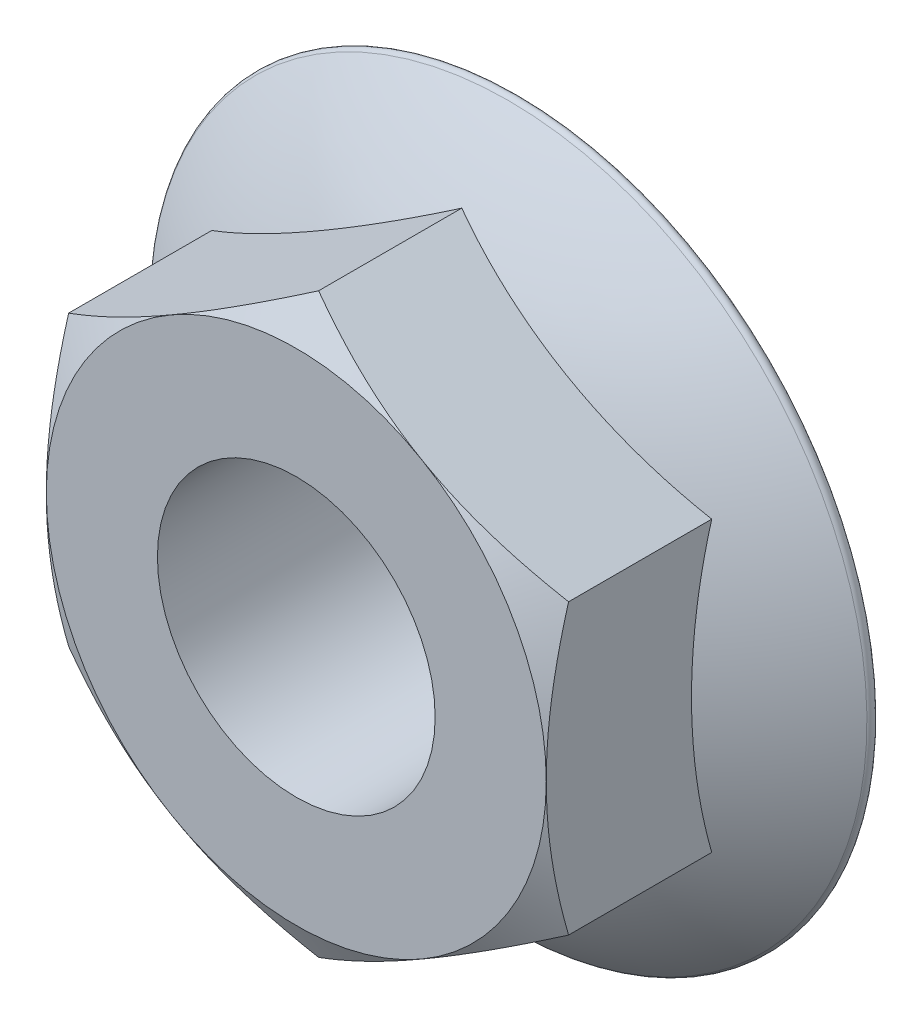
SolidWorks part; units mm, degrees
ref_plane "前视基准面" through (0, 0, 0) normal (0, 0, 1) x (1, 0, 0)
ref_plane "上视基准面" through (0, 0, 0) normal (0, 1, 0) x (1, 0, 0)
ref_plane "右视基准面" through (0, 0, 0) normal (1, 0, 0) x (0, 0, -1)
other "Configuration Table"
sketch "草图1" plane through (0, 0, 0) normal (0, 0, 1) x (1, 0, 0)
  line L1 (22.5, -12.9904) -> (22.5, 12.9904)
  line L2 (22.5, 12.9904) -> (0, 25.9808)
  line L3 (0, 25.9808) -> (-22.5, 12.9904)
  line L4 (-22.5, 12.9904) -> (-22.5, -12.9904)
  line L5 (-22.5, -12.9904) -> (0, -25.9808)
  line L6 (0, -25.9808) -> (22.5, -12.9904)
  circle A0 centre (0, 0) radius 22.5 construction
  dimension "D1" = 45
extrude "凸台-拉伸1" add sketch "草图1" along normal blind 20
sketch "草图2" plane through (0, 0, 0) normal (1, 0, 0) x (0, 0, -1)
  line L0 (0, 0) -> (-12, 0)
  line L1 (0, -31.95) -> (0, 0)
  arc A0 (-12, 0) -> (-0.894, -32.2578) centre (40.4001, 0) ccw
  arc A1 (-0.894, -32.2578) -> (0, -31.95) centre (-0.5, -31.95) ccw
  dimension "D2" = 0.5
  dimension "D1" = 12
  dimension "D3" = 31.95
revolve "旋转1" add sketch "草图2" angle 360 about L0
sketch "草图3" plane through (0, 0, 20) normal (0, 0, 1) x (1, 0, 0)
  circle A0 centre (0, 0) radius 22.5
extrude "切除-拉伸2" cut sketch "草图3" against normal blind 20 draft 60 flip side to cut
sketch "草图4" plane through (0, 0, 20) normal (0, 0, 1) x (1, 0, 0)
  circle A0 centre (0, 0) radius 12.5
  dimension "D1" = 25
extrude "切除-拉伸3" cut sketch "草图4" against normal through all
cosmetic thread "装饰螺纹线1" parameters "D2"=30
